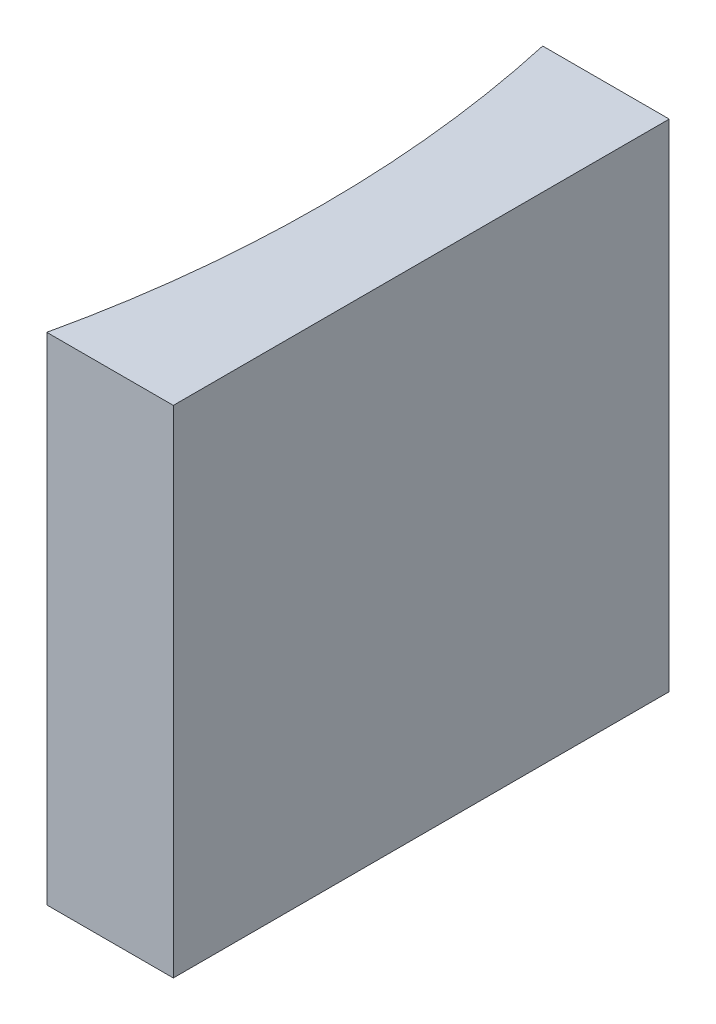
SolidWorks part; units mm, degrees
ref_plane "前视基准面" through (0, 0, 0) normal (0, 0, 1) x (1, 0, 0)
ref_plane "上视基准面" through (0, 0, 0) normal (0, 1, 0) x (1, 0, 0)
ref_plane "右视基准面" through (0, 0, 0) normal (1, 0, 0) x (0, 0, -1)
sketch "草图1" plane through (0, 0, 0) normal (0, 1, 0) x (1, 0, 0)
  line L0 (0, 0) -> (0, -10)
  line L1 (0, 0) -> (-2.552, 0)
  line L2 (0, -10) -> (-2.552, -10)
  line L3 (21.2259, -5) -> (-21.2259, -5) construction
  arc A0 (-2.552, -10) -> (-2.552, 0) centre (-24.92, -5) ccw
  point P7 (-2, -5)
  point P8 (0, -5)
  dimension "D2" = 22.92
  dimension "D3" = 2
  dimension "D1" = 10
extrude "凸台-拉伸1" add sketch "草图1" along normal blind 10
